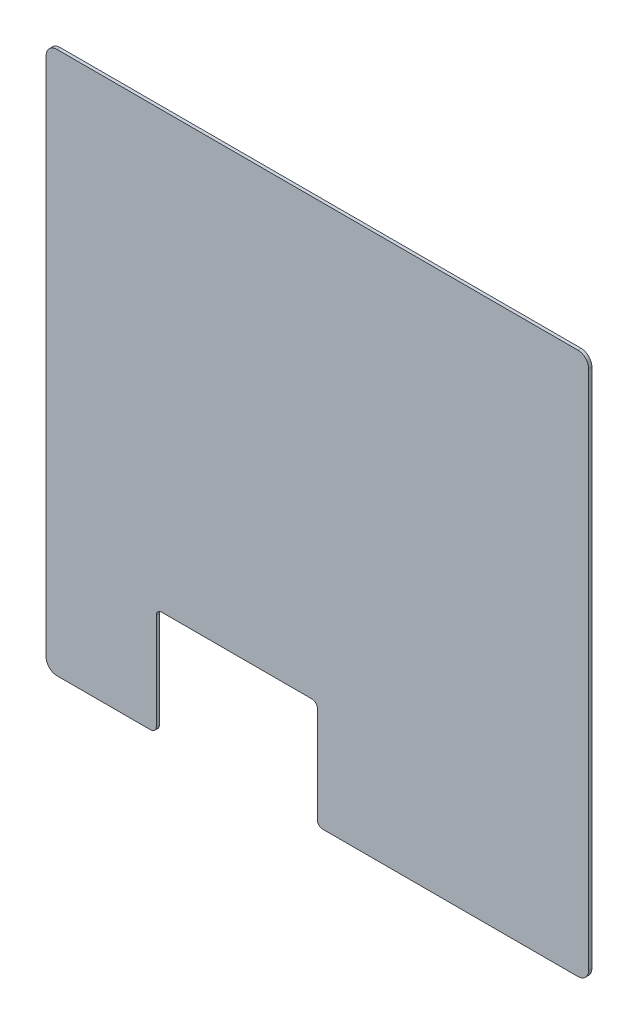
SolidWorks part; units mm, degrees
material "Pine"
ref_plane "Front Plane" through (0, 0, 0) normal (0, 0, 1) x (1, 0, 0)
ref_plane "Top Plane" through (0, 0, 0) normal (0, 1, 0) x (1, 0, 0)
ref_plane "Right Plane" through (0, 0, 0) normal (1, 0, 0) x (0, 0, -1)
sketch "Sketch1" plane through (0, 0, 0) normal (0, 0, 1) x (1, 0, 0)
  line L1 (-500, 500) -> (500, 500) construction
  line L2 (-500, 500) -> (-500, -500) construction
  line L3 (-500, -500) -> (500, -500) construction
  line L4 (500, 500) -> (500, -500) construction
  line L5 (-500, 500) -> (500, -500) construction
  line L6 (-500, -500) -> (500, 500) construction
  line L7 (505, 505) -> (-505, 505)
  line L8 (505, 505) -> (505, -505)
  line L9 (505, -505) -> (-505, -505)
  line L10 (-505, 505) -> (-505, -505)
  line L11 (505, 505) -> (-505, -505) construction
  line L12 (505, -505) -> (-505, 505) construction
  point P0 (0, 0)
  point P5 (0, 0)
  dimension "D1" = 1000
  dimension "D2" = 1000
  dimension "D3" = 1010
extrude "Boss-Extrude1" add sketch "Sketch1" along normal blind 6
sketch "Sketch2" plane through (0, 0, 6) normal (0, 0, 1) x (1, 0, 0)
  line L0 (-505, -505) -> (505, -505) construction
  line L1 (-300, -505) -> (0, -505)
  line L2 (-300, -505) -> (-300, -305)
  line L3 (-300, -305) -> (0, -305)
  line L4 (0, -505) -> (0, -305)
  dimension "D2" = 300
  dimension "D3" = 200
extrude "Cut-Extrude1" cut sketch "Sketch2" against normal blind 6
fillet "Fillet2" radius 20 4 edges at (505, 505, 3) (505, -505, 3) (-505, 505, 3) (-505, -505, 3)
fillet "Fillet3" radius 10 4 edges at (0, -505, 3) (0, -305, 3) (-300, -505, 3) (-300, -305, 3)
sketch "Sketch3" plane through (0, 0, 6) normal (0, 0, 1) x (1, 0, 0)
  line L1 (-250, 250) -> (250, 250)
  line L2 (-250, 250) -> (-250, -250)
  line L3 (-250, -250) -> (250, -250)
  line L4 (250, 250) -> (250, -250)
  line L5 (-250, 250) -> (250, -250) construction
  line L6 (-250, -250) -> (250, 250) construction
  dimension "D1" = 500
